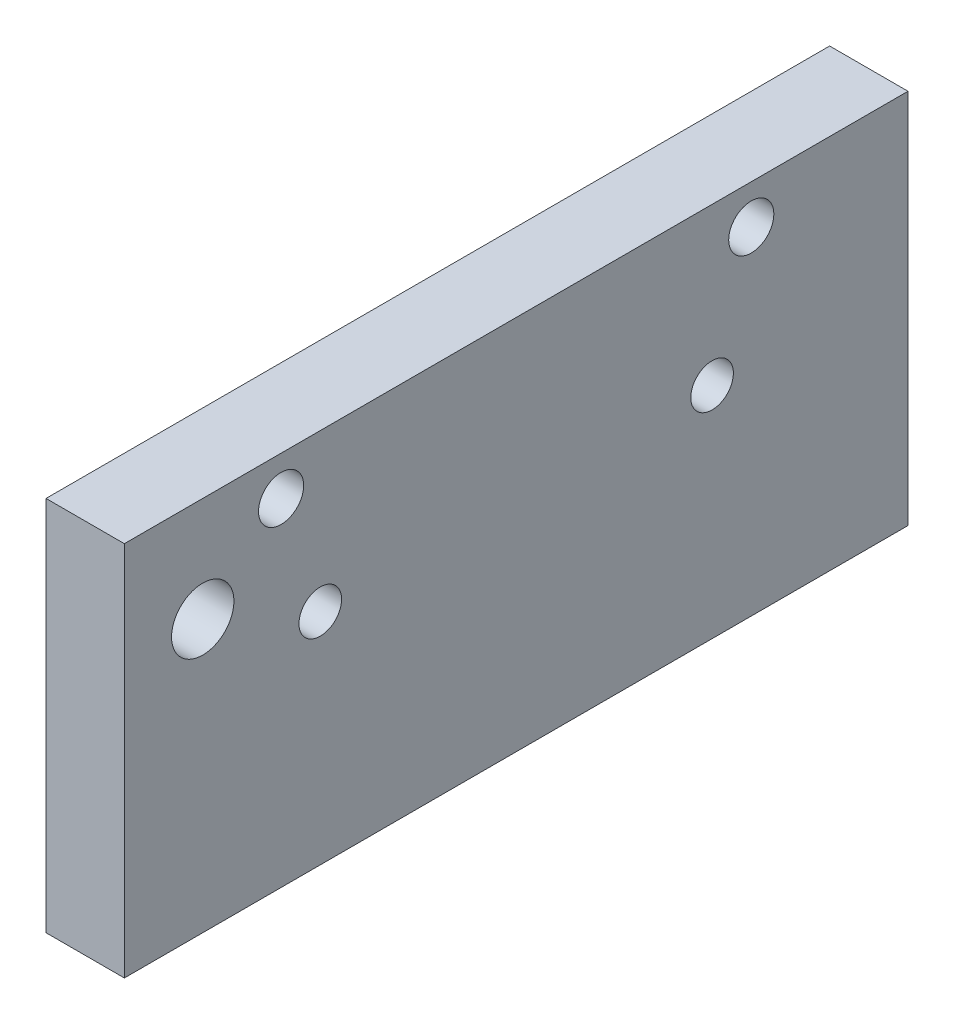
SolidWorks part; units mm, degrees
ref_plane "Front Plane" through (0, 0, 0) normal (0, 0, 1) x (1, 0, 0)
ref_plane "Top Plane" through (0, 0, 0) normal (0, 1, 0) x (1, 0, 0)
ref_plane "Right Plane" through (0, 0, 0) normal (1, 0, 0) x (0, 0, -1)
sketch "Sketch1" plane through (0, 0, 0) normal (1, 0, 0) x (0, 0, -1)
  line L1 (-60.2649, 35.4411) -> (3.2351, 35.4411)
  line L2 (-60.2649, 35.4411) -> (-60.2649, 4.9611)
  line L3 (-60.2649, 4.9611) -> (3.2351, 4.9611)
  line L4 (3.2351, 35.4411) -> (3.2351, 4.9611)
  dimension "D1" = 63.5
  dimension "D2" = 30.48
extrude "Boss-Extrude1" add sketch "Sketch1" along normal blind 6.35
hole_wizard "Tap Drill for #8-32 Tap1" positions "Sketch3" profile "Sketch2" hole size "#8-32" standard "Ansi Inch"
sketch "Sketch3" plane through (0, 0, 0) normal (-1, 0, 0) x (0, 0, 1)
  line L0 (60.2649, 35.4411) -> (60.2649, 4.9611) construction
  line L1 (60.2649, 4.9611) -> (-3.2351, 4.9611) construction
  point P0 (12.6399, 22.7411)
  point P1 (44.3899, 22.7411)
  dimension "D1" = 31.75
  dimension "D2" = 15.875
  dimension "D3" = 17.78
  dimension "D4" = 17.78
sketch "Sketch2" plane through (0, 22.7411, 12.6399) normal (0, 1, 0) x (0, 0, 1)
  line L0 (0, 0) -> (0, 7.3878)
  line L1 (0, 7.3878) -> (1.7272, 6.35)
  line L2 (1.7272, 6.35) -> (1.7272, 0)
  line L5 (1.7272, 0) -> (0, 0)
  line L10 (0, 7.3878) -> (-1.7272, 6.35) construction
  line L11 (0, -6.35) -> (0, 107.95) construction
  dimension "Hole Dia." = 3.4544
  dimension "Hole Depth" = 6.35
  dimension "Drill Angle" = 118
hole_wizard "#6 Close clearance hole, countersink" positions "Sketch7" profile "Sketch6" hole size "#6" standard "Ansi Inch" end condition up to next
sketch "Sketch7" plane through (0, 0, 0) normal (-1, 0, 0) x (0, 0, 1)
  line L0 (-3.2351, 35.4411) -> (60.2649, 35.4411) construction
  line L1 (-3.2351, 4.9611) -> (-3.2351, 35.4411) construction
  point P0 (9.4649, 32.2661)
  point P1 (47.5649, 32.2661)
  dimension "D1" = 3.175
  dimension "D2" = 3.175
  dimension "D3" = 38.1
  dimension "D4" = 12.7
sketch "Sketch6" plane through (0, 32.2661, 9.4649) normal (0, 1, 0) x (0, 0, 1)
  line L0 (0, 0) -> (0, 6.35)
  line L1 (0, 6.35) -> (1.8288, 6.35)
  line L2 (1.8288, 6.35) -> (1.8288, 0)
  line L5 (1.8288, 0) -> (0, 0)
  line L11 (0, -6.35) -> (0, 107.95) construction
  dimension "Thru Hole Dia." = 3.6576
  dimension "Thru Hole Depth" = 6.35
hole_wizard "#8 Through hole" positions "Sketch9" profile "Sketch8" hole size "#8" standard "Ansi Inch"
sketch "Sketch9" plane through (0, 0, 0) normal (-1, 0, 0) x (0, 0, 1)
  line L1 (-3.2351, 35.4411) -> (60.2649, 35.4411) construction
  line L2 (60.2649, 35.4411) -> (60.2649, 4.9611) construction
  point P0 (53.9149, 26.9745)
  dimension "D1" = 6.35
  dimension "D2" = 8.4667
sketch "Sketch8" plane through (0, 26.9745, 53.9149) normal (0, 1, 0) x (0, 0, 1)
  line L0 (0, 0) -> (0, 7.8686)
  line L1 (0, 7.8686) -> (2.5273, 6.35)
  line L2 (2.5273, 6.35) -> (2.5273, 0)
  line L5 (2.5273, 0) -> (0, 0)
  line L10 (0, 7.8686) -> (-2.5273, 6.35) construction
  line L11 (0, -6.35) -> (0, 107.95) construction
  dimension "Hole Dia." = 5.0546
  dimension "Hole Depth" = 6.35
  dimension "Drill Angle" = 118
equation "\"D2@Sketch3\" = (\"D1@Sketch1\"-\"D1@Sketch3\")/2"
equation "\"D4@Sketch7\" =( \"D1@Sketch1\"-\"D3@Sketch7\")/2"
equation "\"D1@Sketch7\" = \"D2@Sketch7\""
equation "\"D4@Sketch3\" = \"D3@Sketch3\""
